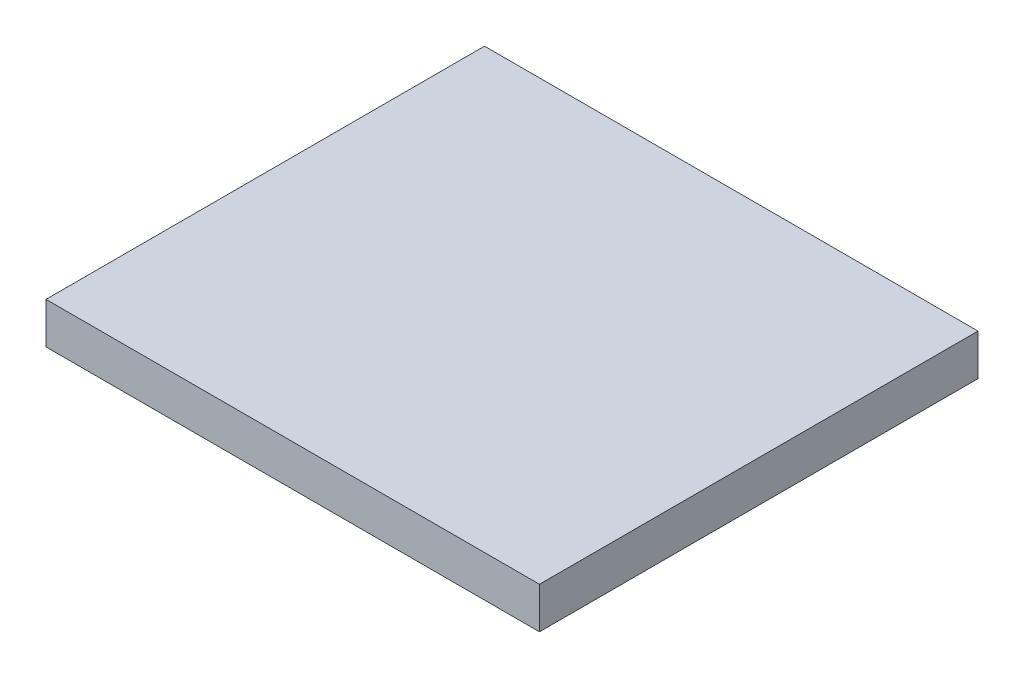
SolidWorks part; units mm, degrees
ref_plane "Front Plane" through (0, 0, 0) normal (0, 0, 1) x (1, 0, 0)
ref_plane "Top Plane" through (0, 0, 0) normal (0, 1, 0) x (1, 0, 0)
ref_plane "Right Plane" through (0, 0, 0) normal (1, 0, 0) x (0, 0, -1)
sketch "Sketch1" plane through (0, 0, 0) normal (0, 1, 0) x (1, 0, 0)
  line L1 (-2737.612, -2432.812) -> (2737.612, -2432.812)
  line L2 (-2737.612, -2432.812) -> (-2737.612, 2432.812)
  line L3 (-2737.612, 2432.812) -> (2737.612, 2432.812)
  line L4 (2737.612, -2432.812) -> (2737.612, 2432.812)
  line L5 (-2737.612, -2432.812) -> (2737.612, 2432.812) construction
  line L6 (-2737.612, 2432.812) -> (2737.612, -2432.812) construction
  point P0 (0, 0)
  dimension "D1" = 4865.624
  dimension "D2" = 5475.224
extrude "Boss-Extrude1" add sketch "Sketch1" along normal blind 457.2
